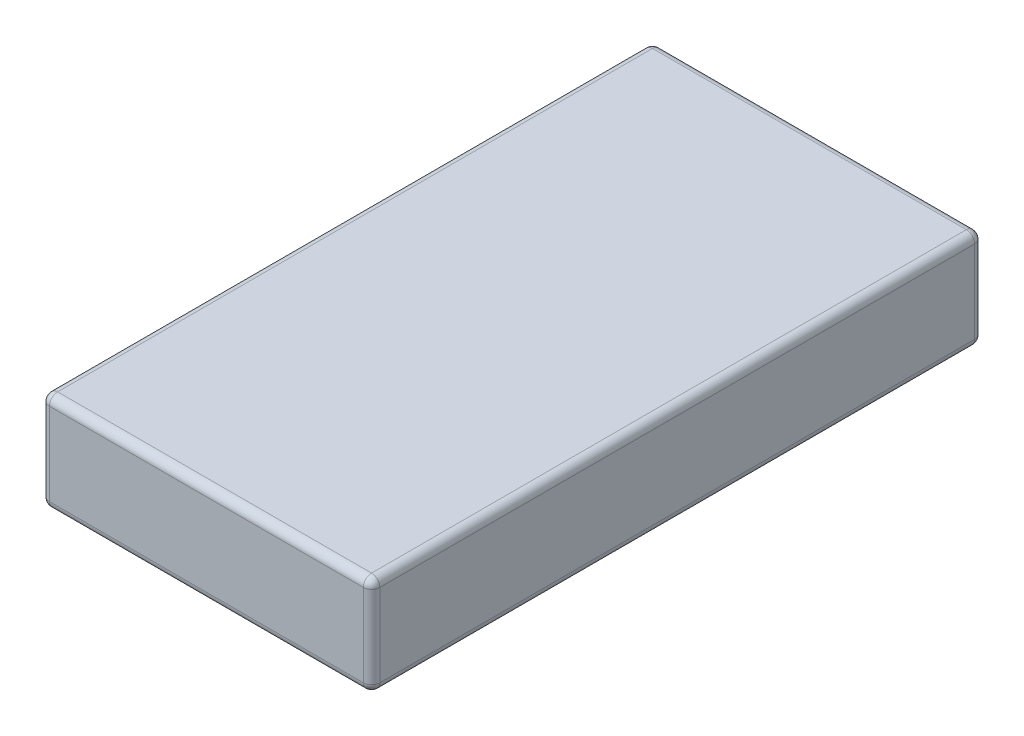
SolidWorks part; units mm, degrees
ref_plane "Front Plane" through (0, 0, 0) normal (0, 0, 1) x (1, 0, 0)
ref_plane "Top Plane" through (0, 0, 0) normal (0, 1, 0) x (1, 0, 0)
ref_plane "Right Plane" through (0, 0, 0) normal (1, 0, 0) x (0, 0, -1)
sketch "Sketch1" plane through (0, 0, 0) normal (0, 1, 0) x (1, 0, 0)
  line L1 (-10, -18.5) -> (10, -18.5)
  line L2 (-10, -18.5) -> (-10, 18.5)
  line L3 (-10, 18.5) -> (10, 18.5)
  line L4 (10, -18.5) -> (10, 18.5)
  line L5 (-10, -18.5) -> (10, 18.5) construction
  line L6 (-10, 18.5) -> (10, -18.5) construction
  point P0 (0, 0)
  dimension "D1" = 20
  dimension "D2" = 37
extrude "Boss-Extrude1" add sketch "Sketch1" along normal blind 6
fillet "Fillet1" radius 0.5 12 edges at (-10, 3, -18.5) (-10, 3, 18.5) (10, 3, 18.5) (10, 3, -18.5) (0, 0, -18.5) (-10, 0, 0) (0, 0, 18.5) (10, 0, 0) (0, 6, 18.5) (-10, 6, 0) (0, 6, -18.5) (10, 6, 0)
